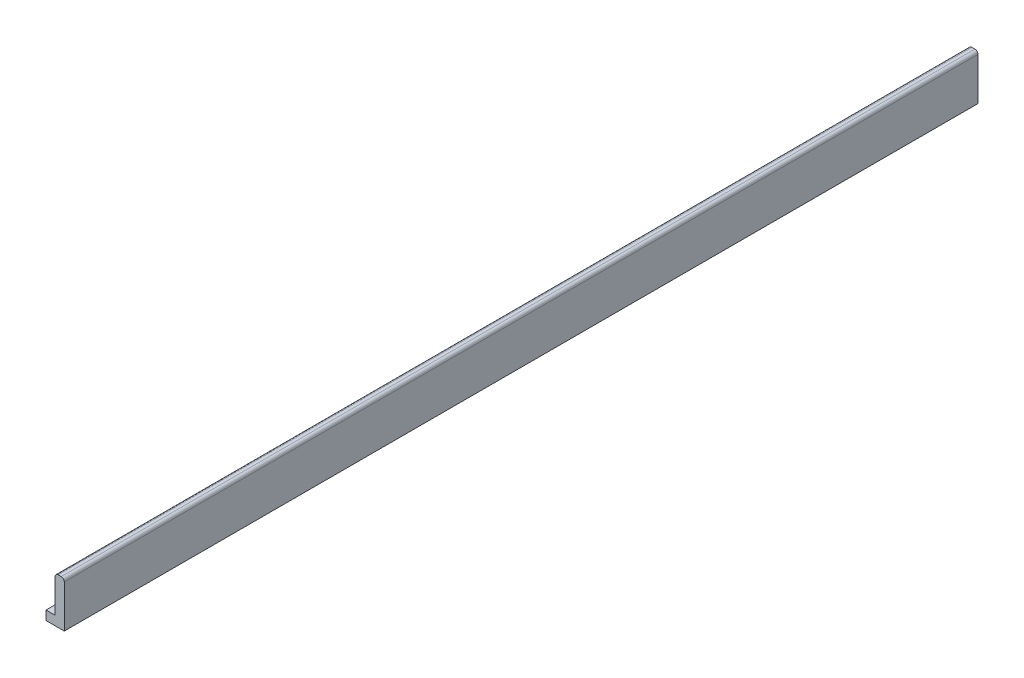
SolidWorks part; units mm, degrees
material "Cedar"
ref_plane "Front Plane" through (0, 0, 0) normal (0, 0, 1) x (1, 0, 0)
ref_plane "Top Plane" through (0, 0, 0) normal (0, 1, 0) x (1, 0, 0)
ref_plane "Right Plane" through (0, 0, 0) normal (1, 0, 0) x (0, 0, -1)
sketch "Sketch1" plane through (0, 0, 0) normal (0, 0, 1) x (1, 0, 0)
  line L0 (0, -75) -> (0, 75)
  line L5 (0, 75) -> (-30, 75)
  line L6 (-30, 75) -> (-30, -45)
  line L7 (-30, -45) -> (-60, -45)
  line L8 (-60, -45) -> (-60, -75)
  line L9 (-60, -75) -> (0, -75)
  dimension "D1" = 150
  dimension "D2" = 30
  dimension "D3" = 30
  dimension "D4" = 30
extrude "Boss-Extrude3" add sketch "Sketch1" along normal blind 3000
fillet "Fillet1" radius 10 2 edges at (-30, 75, 1500) (0, 75, 1500)
